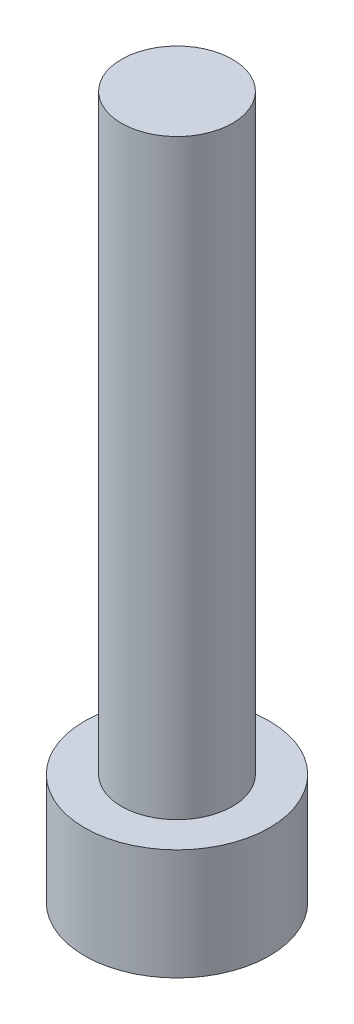
SolidWorks part; units mm, degrees
ref_plane "前视基准面" through (0, 0, 0) normal (0, 0, 1) x (1, 0, 0)
ref_plane "上视基准面" through (0, 0, 0) normal (0, 1, 0) x (1, 0, 0)
ref_plane "右视基准面" through (0, 0, 0) normal (1, 0, 0) x (0, 0, -1)
sketch "草图1" plane through (0, 0, 0) normal (0, 1, 0) x (1, 0, 0)
  circle A0 centre (0, 0) radius 2.5
  dimension "D1" = 5
extrude "凸台-拉伸1" add sketch "草图1" along normal blind 3
sketch "草图2" plane through (0, 3, 0) normal (0, 1, 0) x (1, 0, 0)
  circle A0 centre (0, 0) radius 1.5
extrude "凸台-拉伸2" add sketch "草图2" along normal blind 16
sketch "草图3" plane through (0, 0, 0) normal (0, -1, 0) x (1, 0, 0)
  line L1 (1.425, 0) -> (0.7125, 1.2341)
  line L2 (0.7125, 1.2341) -> (-0.7125, 1.2341)
  line L3 (-0.7125, 1.2341) -> (-1.425, 0)
  line L4 (-1.425, 0) -> (-0.7125, -1.2341)
  line L5 (-0.7125, -1.2341) -> (0.7125, -1.2341)
  line L6 (0.7125, -1.2341) -> (1.425, 0)
  circle A0 centre (0, 0) radius 1.2341 construction
extrude "切除-拉伸1" cut sketch "草图3" against normal blind 1.65
